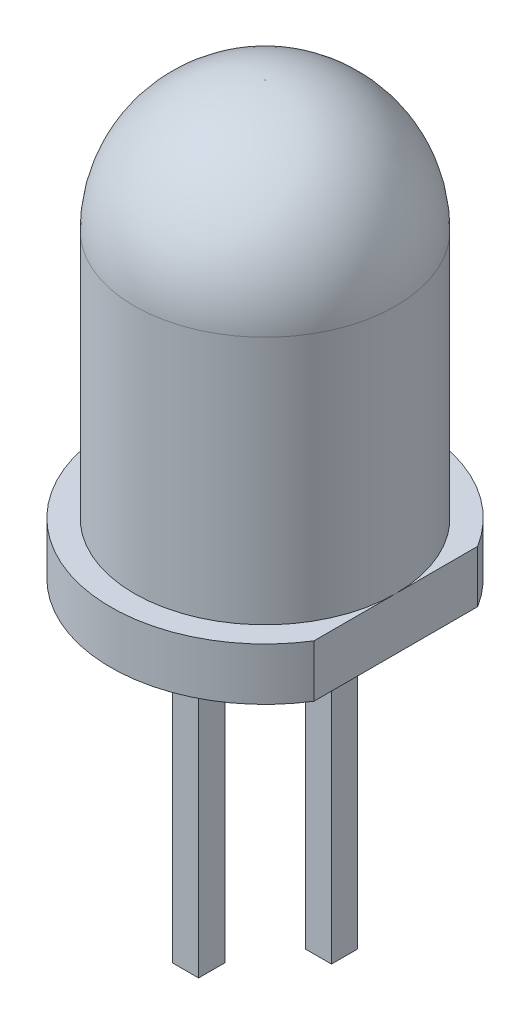
SolidWorks part; units mm, degrees
ref_plane "Alzado" through (0, 0, 0) normal (0, 0, 1) x (1, 0, 0)
ref_plane "Planta" through (0, 0, 0) normal (0, 1, 0) x (1, 0, 0)
ref_plane "Vista lateral" through (0, 0, 0) normal (1, 0, 0) x (0, 0, -1)
sketch "Croquis1" plane through (0, 0, 0) normal (0, 1, 0) x (1, 0, 0)
  circle A0 centre (0, 0) radius 2.95
  dimension "D1" = 5.9
extrude "Base" add sketch "Croquis1" along normal blind 1
sketch "Croquis2" plane through (0, 1, 0) normal (0, 1, 0) x (1, 0, 0)
  circle A0 centre (0, 0) radius 2.5
  dimension "D1" = 5
extrude "Cuerpo del LED" add sketch "Croquis2" along normal blind 7.25
sketch "Croquis3" plane through (0, 0, 0) normal (0, -1, 0) x (1, 0, 0)
  line L0 (-1.2701, 0) -> (0, 0) construction
  line L1 (0, 0) -> (1.2702, 0) construction
  line L2 (-1.5201, -0.25) -> (-1.0201, 0.25) construction
  line L3 (-1.5201, -0.25) -> (-1.0201, -0.25)
  line L4 (-1.5201, -0.25) -> (-1.5201, 0.25)
  line L5 (-1.5201, 0.25) -> (-1.0201, 0.25)
  line L6 (-1.0201, -0.25) -> (-1.0201, 0.25)
  line L7 (1.0202, -0.25) -> (1.5202, 0.25) construction
  line L8 (1.0202, -0.25) -> (1.5202, -0.25)
  line L9 (1.0202, -0.25) -> (1.0202, 0.25)
  line L10 (1.0202, 0.25) -> (1.5202, 0.25)
  line L11 (1.5202, -0.25) -> (1.5202, 0.25)
  dimension "D1" = 0.5
  dimension "D2" = 0.5
  dimension "D3" = 0.5
  dimension "D4" = 0.5
extrude "Pines" add sketch "Croquis3" along normal blind 7 from vertex at 0 starting at point (1.0202, 0, 0.25)
sketch "Croquis4" plane through (0, -7, 0) normal (0, -1, 0) x (1, 0, 0)
  line L4 (1.0202, 0.25) -> (1.0202, -0.25)
  line L5 (1.0202, -0.25) -> (1.5202, -0.25)
  line L6 (1.5202, -0.25) -> (1.5202, 0.25)
  line L7 (1.5202, 0.25) -> (1.0202, 0.25)
  line L8 (1.0202, 0.25) -> (1.0202, -0.25)
  line L9 (1.0202, -0.25) -> (1.5202, -0.25)
  line L10 (1.5202, -0.25) -> (1.5202, 0.25)
  line L11 (1.5202, 0.25) -> (1.0202, 0.25)
  dimension "D1" = 0
extrude "Corte a Catodo" cut sketch "Croquis4" against normal blind 1.5
fillet "Redondeo a Anodo" radius 0.5 4 edges at (-1.5201, 0, 0) (-1.2701, 0, -0.25) (-1.0201, 0, 0) (-1.2701, 0, 0.25)
fillet "Redondeo a Catodo" radius 0.5 4 edges at (1.0202, 0, 0) (1.2702, 0, -0.25) (1.5202, 0, 0) (1.2702, 0, 0.25)
sketch "Croquis6" plane through (0, 1, 0) normal (0, 1, 0) x (1, 0, 0)
  line L0 (2.95, 0) -> (2.5, 0) construction
  line L1 (2.5, 2.7304) -> (2.5, -3.2696)
  line L2 (2.5, -3.2696) -> (3.5, -3.2696)
  line L3 (3.5, -3.2696) -> (3.5, 2.7304)
  line L4 (3.5, 2.7304) -> (2.5, 2.7304)
  circle A0 centre (0, 0) radius 2.95 construction
  circle A1 centre (0, 0) radius 2.5 construction
  dimension "D1" = 6
  dimension "D2" = 1
extrude "Ranura" cut sketch "Croquis6" against normal up to surface (1 mm away) up to face at (1.2702, 0, 0)
fillet "Punta del Led" radius 2.49 1 edges at (0, 8.25, 2.5)
other "PropertyManager"
